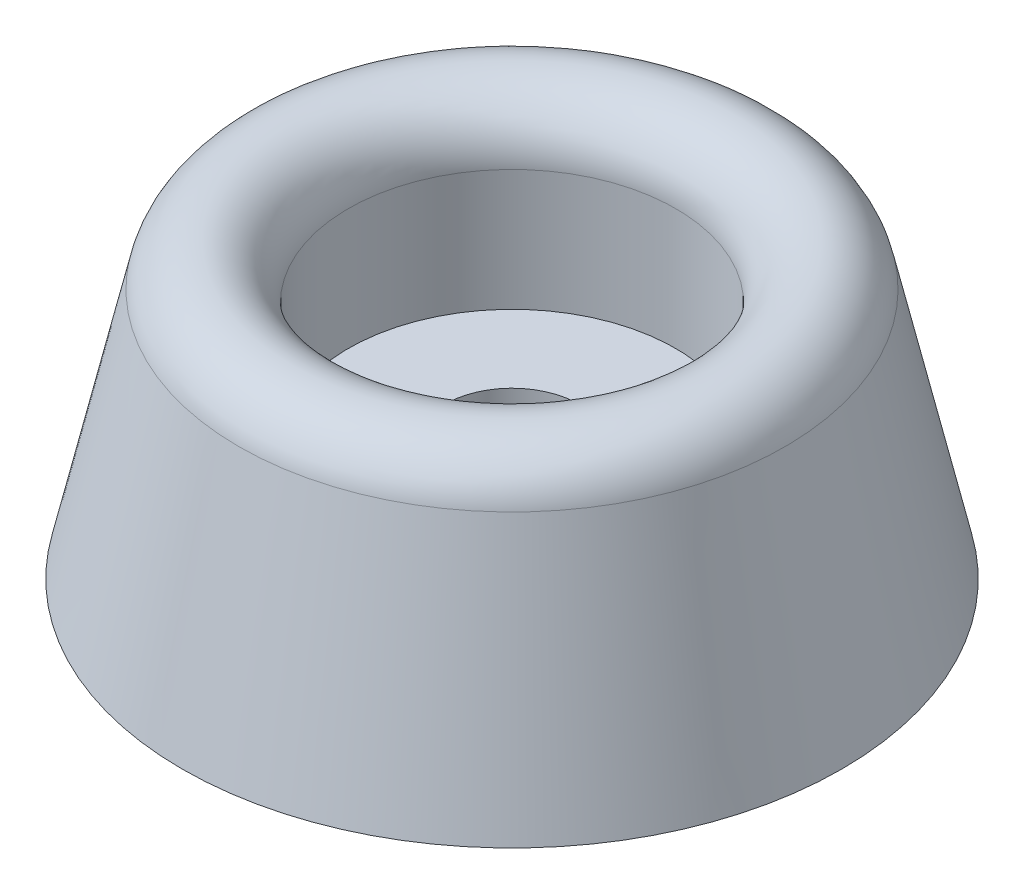
SolidWorks part; units mm, degrees
material "acero"
ref_plane "Alzado" through (0, 0, 0) normal (0, 0, 1) x (1, 0, 0)
ref_plane "Planta" through (0, 0, 0) normal (0, 1, 0) x (1, 0, 0)
ref_plane "Vista lateral" through (0, 0, 0) normal (1, 0, 0) x (0, 0, -1)
ref_plane "Plano1" through (0, 0, 0) normal (0, 0, -1) x (-1, 0, 0)
sketch "Croquis1" plane through (0, 0, 0) normal (0, 0, -1) x (-1, 0, 0)
  line L0 (-1.6, 0) -> (-1.6, 2.8)
  line L1 (-1.6, 2.8) -> (-3.9, 2.8)
  line L2 (-3.9, 2.8) -> (-3.9, 5.6838)
  line L3 (-6.5, 5.9739) -> (-7.85, 0)
  line L4 (-7.85, 0) -> (-1.6, 0)
  line L5 (0, 0) -> (0, 7) construction
  arc A0 (-3.9, 5.6838) -> (-6.5, 5.9739) centre (-5.2162, 5.6838) ccw
revolve "Revolución1" add sketch "Croquis1" angle 360 about L5
